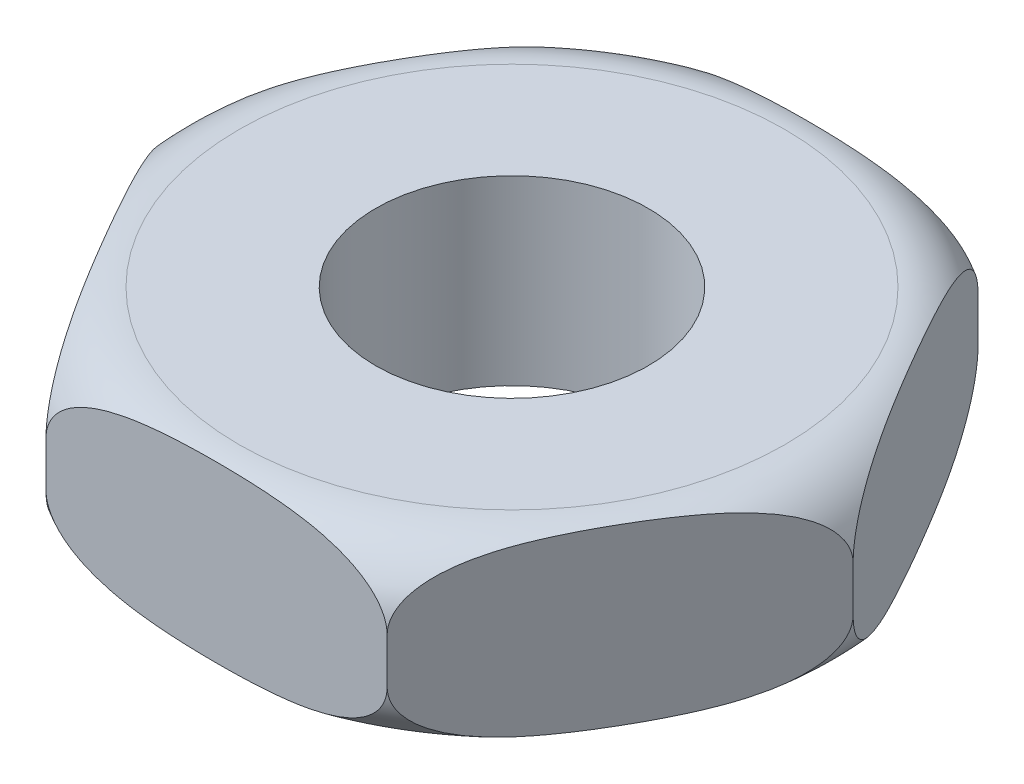
SolidWorks part; units mm, degrees
ref_plane "Front Plane" through (0, 0, 0) normal (0, 0, 1) x (1, 0, 0)
ref_plane "Top Plane" through (0, 0, 0) normal (0, 1, 0) x (1, 0, 0)
ref_plane "Right Plane" through (0, 0, 0) normal (1, 0, 0) x (0, 0, -1)
sketch "Sketch1" plane through (0, 0, 0) normal (0, 1, 0) x (1, 0, 0)
  line L1 (15.0111, 0) -> (7.5056, 13)
  line L2 (7.5056, 13) -> (-7.5056, 13)
  line L3 (-7.5056, 13) -> (-15.0111, 0)
  line L4 (-15.0111, 0) -> (-7.5056, -13)
  line L5 (-7.5056, -13) -> (7.5056, -13)
  line L6 (7.5056, -13) -> (15.0111, 0)
  circle A0 centre (0, 0) radius 13 construction
  circle A1 centre (0, 0) radius 6
  dimension "D2" = 12
  dimension "D1" = 26
extrude "Boss-Extrude1" add sketch "Sketch1" along normal mid plane 8
sketch "Sketch2" plane through (0, 0, 0) normal (0, 0, 1) x (1, 0, 0)
  line L0 (15.0111, 4) -> (15.0111, -4) construction
  line L1 (7.5056, 4) -> (15.0111, 4) construction
  line L2 (15.0111, 1) -> (15.0111, 4)
  line L3 (15.0111, 4) -> (12.0111, 4)
  line L4 (0, 7.2945) -> (0, -6.0289) construction
  arc A0 (15.0111, 1) -> (12.0111, 4) centre (12.0111, 1) ccw
  dimension "D1" = 3
revolve "Cut-Revolve1" cut sketch "Sketch2" angle 360 about L4
mirror "Mirror1" about plane through (0, 0, 0) normal (0, 1, 0) of "Cut-Revolve1"
